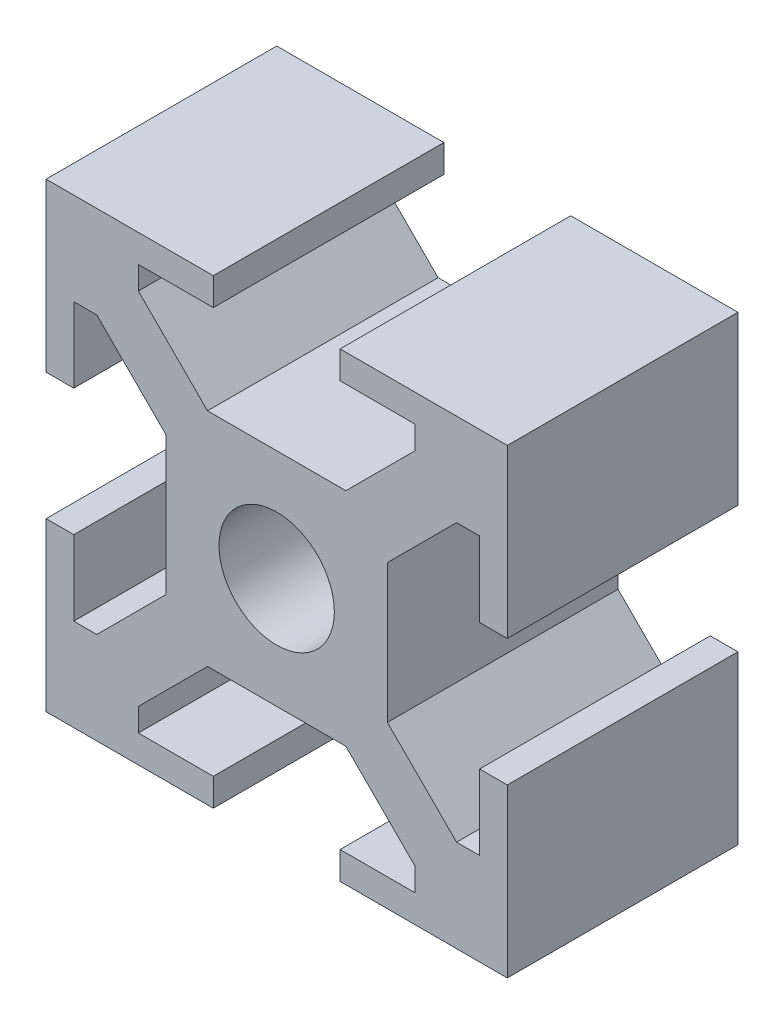
SolidWorks part; units mm, degrees
ref_plane "Plan de face" through (0, 0, 0) normal (0, 0, 1) x (1, 0, 0)
ref_plane "Plan de dessus" through (0, 0, 0) normal (0, 1, 0) x (1, 0, 0)
ref_plane "Plan de droite" through (0, 0, 0) normal (1, 0, 0) x (0, 0, -1)
sketch "Esquisse1" plane through (0, 0, 0) normal (0, 0, 1) x (1, 0, 0)
  line L1 (-22.5051, 0.0904) -> (-2.5051, 0.0904)
  line L2 (-22.5051, 0.0904) -> (-22.5051, -19.9096)
  line L3 (-22.5051, -19.9096) -> (-2.5051, -19.9096)
  line L4 (-2.5051, 0.0904) -> (-2.5051, -19.9096)
  dimension "D1" = 20
  dimension "D2" = 20
extrude "Boss.-Extru.1" add sketch "Esquisse1" along normal blind 10
sketch "Esquisse2" plane through (0, 0, 10) normal (0, 0, 1) x (1, 0, 0)
  line L0 (-22.5051, 0.0904) -> (-22.5051, -19.9096) construction
  line L1 (-22.5051, -7.1596) -> (-21.3051, -7.1596)
  line L2 (-22.5051, -7.1596) -> (-22.5051, -12.6596)
  line L3 (-22.5051, -12.6596) -> (-21.3051, -12.6596)
  line L4 (-21.3051, -7.1596) -> (-21.3051, -12.6596)
  line L5 (-2.5051, 0.0904) -> (-22.5051, 0.0904) construction
  line L6 (-15.2551, 0.0904) -> (-9.7551, 0.0904)
  line L7 (-15.2551, 0.0904) -> (-15.2551, -1.1096)
  line L8 (-15.2551, -1.1096) -> (-9.7551, -1.1096)
  line L9 (-9.7551, 0.0904) -> (-9.7551, -1.1096)
  line L10 (-2.5051, -19.9096) -> (-2.5051, 0.0904) construction
  line L11 (-2.5051, -7.1596) -> (-3.7051, -7.1596)
  line L12 (-2.5051, -7.1596) -> (-2.5051, -12.6596)
  line L13 (-2.5051, -12.6596) -> (-3.7051, -12.6596)
  line L14 (-3.7051, -7.1596) -> (-3.7051, -12.6596)
  line L15 (-22.5051, -19.9096) -> (-2.5051, -19.9096) construction
  line L16 (-15.2551, -19.9096) -> (-9.7551, -19.9096)
  line L17 (-15.2551, -19.9096) -> (-15.2551, -18.7096)
  line L18 (-15.2551, -18.7096) -> (-9.7551, -18.7096)
  line L19 (-9.7551, -19.9096) -> (-9.7551, -18.7096)
  dimension "D1" = 1.2
  dimension "D2" = 1.2
  dimension "D3" = 1.2
  dimension "D4" = 1.2
  dimension "D5" = 5.5
  dimension "D6" = 5.5
  dimension "D7" = 5.5
  dimension "D8" = 5.5
  dimension "D9" = 7.25
  dimension "D10" = 7.25
  dimension "D11" = 7.25
  dimension "D12" = 7.25
extrude "Enlèv. mat.-Extru.1" cut sketch "Esquisse2" against normal through all
sketch "Esquisse3" plane through (0, 0, 10) normal (0, 0, 1) x (1, 0, 0)
  line L0 (-15.2551, 0.0904) -> (-22.5051, 0.0904) construction
  line L1 (-21.3051, -15.9096) -> (-20.3051, -15.9096)
  line L2 (-21.3051, -15.9096) -> (-21.3051, -3.9096)
  line L3 (-21.3051, -3.9096) -> (-20.3051, -3.9096)
  line L4 (-17.3051, -12.9096) -> (-17.3051, -6.9096)
  line L5 (-18.5051, -1.1096) -> (-6.5051, -1.1096)
  line L6 (-18.5051, -1.1096) -> (-18.5051, -2.1096)
  line L7 (-15.5051, -5.1096) -> (-9.5051, -5.1096)
  line L8 (-6.5051, -1.1096) -> (-6.5051, -2.1096)
  line L9 (-3.7051, -3.9096) -> (-4.7051, -3.9096)
  line L10 (-3.7051, -3.9096) -> (-3.7051, -15.9096)
  line L11 (-3.7051, -15.9096) -> (-4.7051, -15.9096)
  line L12 (-7.7051, -6.9096) -> (-7.7051, -12.9096)
  line L13 (-6.5051, -18.7096) -> (-18.5051, -18.7096)
  line L14 (-6.5051, -18.7096) -> (-6.5051, -17.7096)
  line L15 (-9.5051, -14.7096) -> (-15.5051, -14.7096)
  line L16 (-18.5051, -18.7096) -> (-18.5051, -17.7096)
  line L17 (-2.5051, -7.1596) -> (-2.5051, 0.0904) construction
  line L18 (-15.2551, -1.1096) -> (-9.7551, -1.1096) construction
  line L19 (-3.7051, -7.1596) -> (-3.7051, -12.6596) construction
  line L20 (-9.7551, -19.9096) -> (-2.5051, -19.9096) construction
  line L21 (-22.5051, -12.6596) -> (-22.5051, -19.9096) construction
  line L22 (-22.5051, -19.9096) -> (-15.2551, -19.9096) construction
  line L23 (-15.5051, -14.7096) -> (-18.5051, -17.7096)
  line L24 (-20.3051, -15.9096) -> (-17.3051, -12.9096)
  line L25 (-6.5051, -17.7096) -> (-9.5051, -14.7096)
  line L26 (-4.7051, -15.9096) -> (-7.7051, -12.9096)
  line L27 (-4.7051, -3.9096) -> (-7.7051, -6.9096)
  line L28 (-9.5051, -5.1096) -> (-6.5051, -2.1096)
  line L29 (-18.5051, -2.1096) -> (-15.5051, -5.1096)
  line L30 (-20.3051, -3.9096) -> (-17.3051, -6.9096)
  point P1 (-17.3051, -3.9096)
  point P3 (-17.3051, -15.9096)
  point P5 (-6.5051, -5.1096)
  point P6 (-18.5051, -5.1096)
  point P9 (-7.7051, -15.9096)
  point P11 (-7.7051, -3.9096)
  point P13 (-18.5051, -14.7096)
  point P14 (-6.5051, -14.7096)
  point P24 (-6.1301, -19.9096)
  dimension "D1" = 4
  dimension "D2" = 4
  dimension "D3" = 4
  dimension "D4" = 4
  dimension "D5" = 12
  dimension "D6" = 4
  dimension "D7" = 12
  dimension "D8" = 4
  dimension "D9" = 0
  dimension "D10" = 0
  dimension "D11" = 4
  dimension "D12" = 12
  dimension "D13" = 12
  dimension "D14" = 4
  dimension "D15" = 1.2
  dimension "D16" = 1.2
  dimension "D17" = 3
  dimension "D18" = 3
  dimension "D19" = 3
  dimension "D20" = 3
  dimension "D21" = 3
  dimension "D22" = 3
  dimension "D23" = 3
  dimension "D24" = 3
  dimension "D25" = 3
  dimension "D26" = 3
  dimension "D27" = 3
  dimension "D28" = 3
  dimension "D29" = 3
  dimension "D30" = 3
  dimension "D31" = 3
  dimension "D32" = 3
extrude "Enlèv. mat.-Extru.2" cut sketch "Esquisse3" against normal through all
sketch "Esquisse4" plane through (0, 0, 10) normal (0, 0, 1) x (1, 0, 0)
  line L0 (-15.5051, -5.1096) -> (-9.5051, -5.1096) construction
  line L2 (-17.3051, -12.9096) -> (-17.3051, -6.9096) construction
  circle A0 centre (-12.5051, -9.9096) radius 2.5
  dimension "D1" = 5
  dimension "D2" = 4.8
  dimension "D3" = 4.8
extrude "Enlèv. mat.-Extru.3" cut sketch "Esquisse4" against normal through all
